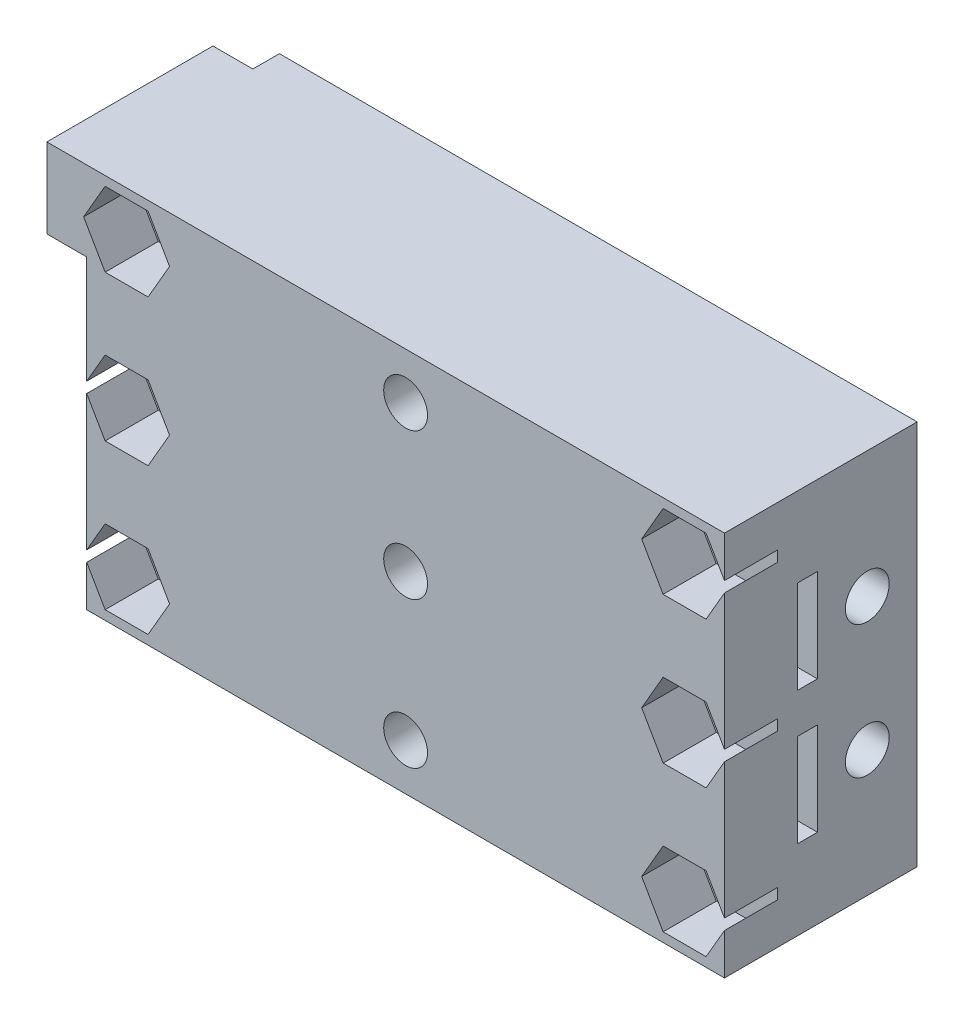
SolidWorks part; units mm, degrees
ref_plane "Plano frontal" through (0, 0, 0) normal (0, 0, 1) x (1, 0, 0)
ref_plane "Plano superior" through (0, 0, 0) normal (0, 1, 0) x (1, 0, 0)
ref_plane "Plano direito" through (0, 0, 0) normal (1, 0, 0) x (0, 0, -1)
sketch "Esboço1" plane through (0, 0, 0) normal (0, 0, 1) x (1, 0, 0)
  line L0 (-24, 0) -> (0, 0) construction
  line L1 (-24, 14.5) -> (24, 14.5)
  line L2 (-24, 14.5) -> (-24, -14.5)
  line L3 (-24, -14.5) -> (24, -14.5)
  line L4 (24, 14.5) -> (24, -14.5)
  line L5 (-24, 14.5) -> (24, -14.5) construction
  line L6 (-24, -14.5) -> (24, 14.5) construction
  line L7 (0, 0) -> (0, 14.5) construction
  circle A0 centre (-21, 11) radius 1.65
  circle A1 centre (-21, -11) radius 1.65
  circle A2 centre (21, -11) radius 1.65
  circle A3 centre (21, 11) radius 1.65
  point P0 (0, 0)
  dimension "D1" = 3.3
  dimension "D2" = 29
  dimension "D3" = 22
  dimension "D4" = 48
  dimension "D5" = 3
extrude "Ressalto-extrusão1" add sketch "Esboço1" along normal blind 12
sketch "Esboço2" plane through (0, 0, 0) normal (0, 1, 0) x (1, 0, 0)
  line L0 (-24, -9) -> (-8, -9)
  line L1 (-24, -12) -> (-24, 0) construction
  line L2 (24, 0) -> (-24, 0) construction
  line L3 (-18, 0) -> (-3.5, 0)
  line L4 (-18, 0) -> (-18, -7.5)
  line L5 (-18, -7.5) -> (-24, -7.5)
  line L6 (-24, -7.5) -> (-24, -9)
  line L8 (0, 0) -> (0, -12) construction
  line L9 (24, -12) -> (-24, -12) construction
  line L11 (24, -7.5) -> (24, -9)
  line L12 (18, -7.5) -> (24, -7.5)
  line L13 (18, 0) -> (18, -7.5)
  line L14 (24, -9) -> (8, -9)
  line L15 (3.5, -4.5) -> (3.5, 0)
  line L16 (-3.5, -4.5) -> (-3.5, 0)
  line L17 (3.5, 0) -> (18, 0)
  arc A0 (-8, -9) -> (-3.5, -4.5) centre (-8, -4.5) ccw
  arc A1 (8, -9) -> (3.5, -4.5) centre (8, -4.5) cw
  circle A2 centre (-23, 0) radius 0.6
  circle A3 centre (-21, 0) radius 0.6
  circle A4 centre (-19, 0) radius 0.6
  circle A5 centre (19, 0) radius 0.6
  circle A6 centre (21, 0) radius 0.6
  circle A7 centre (23, 0) radius 0.6
  dimension "D5" = 1.2
  dimension "D1" = 3
  dimension "D2" = 1.5
  dimension "D3" = 16
  dimension "D4" = 6
  dimension "D7" = 1
  dimension "D6" = 3
extrude "Corte-extrusão3" cut sketch "Esboço2" along normal blind 7 from offset 1.5
mirror "Espelhar1" about plane through (0, 0, 0) normal (0, 1, 0) of "Corte-extrusão3"
sketch "Esboço3" plane through (24, 0, 0) normal (1, 0, 0) x (0, 0, -1)
  line L0 (-7.5, -8.5) -> (-7.5, -1.5) construction
  line L1 (0, 0) -> (-12, 0) construction
  line L2 (-12, -14.5) -> (-12, 14.5) construction
  line L3 (-7.5, 5) -> (0, 5) construction
  line L4 (-7.5, 8.5) -> (-7.5, 1.5) construction
  line L5 (0, -14.5) -> (0, 14.5) construction
  circle A0 centre (-3.75, 5) radius 1.65
  circle A1 centre (-3.75, -5) radius 1.65
  point P7 (-7.5, -5)
  point P19 (-3.75, 5)
  dimension "D1" = 3.3
extrude "Corte-extrusão4" cut sketch "Esboço3" against normal blind 16
sketch "Esboço4" plane through (18, 0, 0) normal (-1, 0, 0) x (0, 0, 1)
  line L1 (6.9254, 5) -> (5.3377, 7.75)
  line L2 (5.3377, 7.75) -> (2.1623, 7.75)
  line L3 (2.1623, 7.75) -> (0.5746, 5)
  line L4 (0.5746, 5) -> (2.1623, 2.25)
  line L5 (2.1623, 2.25) -> (5.3377, 2.25)
  line L6 (5.3377, 2.25) -> (6.9254, 5)
  line L7 (6.9254, -5) -> (5.3377, -2.25)
  line L8 (5.3377, -2.25) -> (2.1623, -2.25)
  line L9 (2.1623, -2.25) -> (0.5746, -5)
  line L10 (0.5746, -5) -> (2.1623, -7.75)
  line L11 (2.1623, -7.75) -> (5.3377, -7.75)
  line L12 (5.3377, -7.75) -> (6.9254, -5)
  circle A0 centre (3.75, 5) radius 2.75 construction
  circle A1 centre (3.75, -5) radius 2.75 construction
  dimension "D1" = 5.5
extrude "Corte-extrusão5" cut sketch "Esboço4" against normal blind 2
sketch "Esboço5" plane through (24, 0, 0) normal (1, 0, 0) x (0, 0, -1)
  line L1 (-6.5, 2.75) -> (-3.5, 2.75)
  line L2 (-6.5, 2.75) -> (-6.5, -2.75)
  line L3 (-6.5, -2.75) -> (-3.5, -2.75)
  line L4 (-3.5, 2.75) -> (-3.5, -2.75)
  line L5 (-6.5, 2.75) -> (-3.5, -2.75) construction
  line L6 (-6.5, -2.75) -> (-3.5, 2.75) construction
  line L7 (-6.5, 8.25) -> (-3.5, 8.25)
  line L8 (-6.5, 8.25) -> (-6.5, 13.75)
  line L9 (-6.5, 13.75) -> (-3.5, 13.75)
  line L10 (-3.5, 8.25) -> (-3.5, 13.75)
  line L11 (-6.5, 8.25) -> (-3.5, 13.75) construction
  line L12 (-6.5, 13.75) -> (-3.5, 8.25) construction
  line L14 (-6.5, -8.25) -> (-3.5, -8.25)
  line L15 (-6.5, -8.25) -> (-6.5, -13.75)
  line L16 (-6.5, -13.75) -> (-3.5, -13.75)
  line L17 (-3.5, -8.25) -> (-3.5, -13.75)
  line L18 (-6.5, -8.25) -> (-3.5, -13.75) construction
  line L19 (-6.5, -13.75) -> (-3.5, -8.25) construction
  line L20 (0, 0) -> (-12, 0) construction
  line L21 (-12, -14.5) -> (-12, 14.5) construction
  point P0 (-5, 0)
  point P5 (-5, 11)
  point P12 (-5, -11)
  point P20 (-3.75, 5)
  dimension "D1" = 5.5
  dimension "D2" = 3
  dimension "D3" = 5
  dimension "D4" = 22
extrude "Corte-extrusão6" [suppressed] cut sketch "Esboço5" against normal blind 7
sketch "Esboço6" plane through (0, 0, 0) normal (0, 0, -1) x (-1, 0, 0)
  line L0 (0, 0) -> (0, -14.5) construction
  line L1 (24, -14.5) -> (-24, -14.5) construction
  line L2 (0, 0) -> (-9.4505, 0) construction
  circle A0 centre (-21, 0) radius 1.65
  circle A1 centre (21, 0) radius 1.65
  circle A2 centre (0, 0) radius 1.65
  circle A3 centre (0, 11) radius 1.65
  circle A4 centre (0, -11) radius 1.65
  point P3 (-21, 11)
  dimension "D1" = 3.3
extrude "Corte-extrusão7" cut sketch "Esboço6" against normal through all
mirror "Espelhar2" about plane through (0, 0, 0) normal (1, 0, 0) of "Corte-extrusão6", "Corte-extrusão5", "Corte-extrusão4"
sketch "Esboço7" plane through (0, 0, 0) normal (0, 0, -1) x (-1, 0, 0)
  circle A0 centre (0, 11) radius 3.4
  circle A1 centre (0, 0) radius 3.4
  circle A2 centre (0, -11) radius 3.4
  dimension "D1" = 6.8
extrude "Corte-extrusão9" cut sketch "Esboço7" against normal blind 3
sketch "Esboço9" plane through (0, 0, 12) normal (0, 0, 1) x (1, 0, 0)
  line L1 (-24, 14.5) -> (-27, 14.5)
  line L2 (-24, 14.5) -> (-24, 8.5)
  line L3 (-24, 8.5) -> (-27, 8.5)
  line L4 (-27, 14.5) -> (-27, 8.5)
  dimension "D1" = 3
  dimension "D2" = 6
extrude "Ressalto-extrusão2" add sketch "Esboço9" against normal blind 10
sketch "Esboço11" plane through (0, 0, 12) normal (0, 0, 1) x (1, 0, 0)
  line L6 (24, -14.5) -> (24, 14.5)
  line L7 (24, 14.5) -> (-27, 14.5)
  line L8 (-27, 14.5) -> (-27, 8.5)
  line L9 (-27, 8.5) -> (-24, 8.5)
  line L10 (-24, 8.5) -> (-24, -14.5)
  line L11 (-24, -14.5) -> (24, -14.5)
  line L12 (24, -14.5) -> (24, 14.5)
  line L13 (24, 14.5) -> (-27, 14.5)
  line L14 (-27, 14.5) -> (-27, 8.5)
  line L15 (-27, 8.5) -> (-24, 8.5)
  line L16 (-24, 8.5) -> (-24, -14.5)
  line L17 (-24, -14.5) -> (24, -14.5)
  circle A0 centre (-21, 11) radius 1.65 construction
  circle A1 centre (-21, 0) radius 1.65 construction
  circle A2 centre (0, 11) radius 1.65 construction
  circle A3 centre (0, 0) radius 1.65 construction
  circle A4 centre (21, 11) radius 1.65 construction
  circle A5 centre (21, 0) radius 1.65 construction
  circle A6 centre (21, -11) radius 1.65 construction
  circle A7 centre (0, -11) radius 1.65 construction
  circle A8 centre (-21, -11) radius 1.65 construction
  circle A9 centre (-21, -11) radius 1.65
  circle A10 centre (0, -11) radius 1.65
  circle A11 centre (21, -11) radius 1.65
  circle A12 centre (21, 0) radius 1.65
  circle A13 centre (21, 11) radius 1.65
  circle A14 centre (0, 0) radius 1.65
  circle A15 centre (0, 11) radius 1.65
  circle A16 centre (-21, 0) radius 1.65
  circle A17 centre (-21, 11) radius 1.65
  dimension "D1" = 0
extrude "Ressalto-extrusão3" add sketch "Esboço11" along normal blind 2.5
sketch "Esboço8" plane through (0, 0, 14.5) normal (0, 0, 1) x (1, 0, 0)
  line L0 (0, 15.9572) -> (0, 0) construction
  line L1 (24.2332, 11) -> (22.6166, 13.8)
  line L2 (22.6166, 13.8) -> (19.3834, 13.8)
  line L3 (19.3834, 13.8) -> (17.7668, 11)
  line L4 (17.7668, 11) -> (19.3834, 8.2)
  line L5 (19.3834, 8.2) -> (22.6166, 8.2)
  line L6 (22.6166, 8.2) -> (24.2332, 11)
  line L7 (0, 0) -> (7.0932, 0) construction
  line L8 (-22.6166, 8.2) -> (-24.2332, 11)
  line L9 (-19.3834, 8.2) -> (-22.6166, 8.2)
  line L10 (-17.7668, 11) -> (-19.3834, 8.2)
  line L11 (-19.3834, 13.8) -> (-17.7668, 11)
  line L12 (-22.6166, 13.8) -> (-19.3834, 13.8)
  line L13 (-24.2332, 11) -> (-22.6166, 13.8)
  line L14 (-24.2332, -11) -> (-22.6166, -13.8)
  line L15 (-22.6166, -13.8) -> (-19.3834, -13.8)
  line L16 (-19.3834, -13.8) -> (-17.7668, -11)
  line L17 (-17.7668, -11) -> (-19.3834, -8.2)
  line L18 (-19.3834, -8.2) -> (-22.6166, -8.2)
  line L19 (-22.6166, -8.2) -> (-24.2332, -11)
  line L20 (22.6166, -8.2) -> (24.2332, -11)
  line L21 (19.3834, -8.2) -> (22.6166, -8.2)
  line L22 (17.7668, -11) -> (19.3834, -8.2)
  line L23 (19.3834, -13.8) -> (17.7668, -11)
  line L24 (22.6166, -13.8) -> (19.3834, -13.8)
  line L25 (24.2332, -11) -> (22.6166, -13.8)
  line L26 (-22.6166, -2.8) -> (-24.2332, 0)
  line L27 (24.2332, 0) -> (22.6166, 2.8)
  line L28 (22.6166, 2.8) -> (19.3834, 2.8)
  line L29 (19.3834, 2.8) -> (17.7668, 0)
  line L30 (17.7668, 0) -> (19.3834, -2.8)
  line L31 (19.3834, -2.8) -> (22.6166, -2.8)
  line L32 (22.6166, -2.8) -> (24.2332, 0)
  line L33 (-19.3834, -2.8) -> (-22.6166, -2.8)
  line L34 (-17.7668, 0) -> (-19.3834, -2.8)
  line L35 (-19.3834, 2.8) -> (-17.7668, 0)
  line L36 (-22.6166, 2.8) -> (-19.3834, 2.8)
  line L37 (-24.2332, 0) -> (-22.6166, 2.8)
  circle A0 centre (21, 11) radius 2.8 construction
  circle A1 centre (-21, 11) radius 2.8 construction
  circle A2 centre (-21, -11) radius 2.8 construction
  circle A3 centre (21, -11) radius 2.8 construction
  circle A4 centre (21, 0) radius 2.8 construction
  circle A5 centre (-21, 0) radius 2.8 construction
  dimension "D1" = 5.6
extrude "Corte-extrusão10" cut sketch "Esboço8" against normal blind 4
